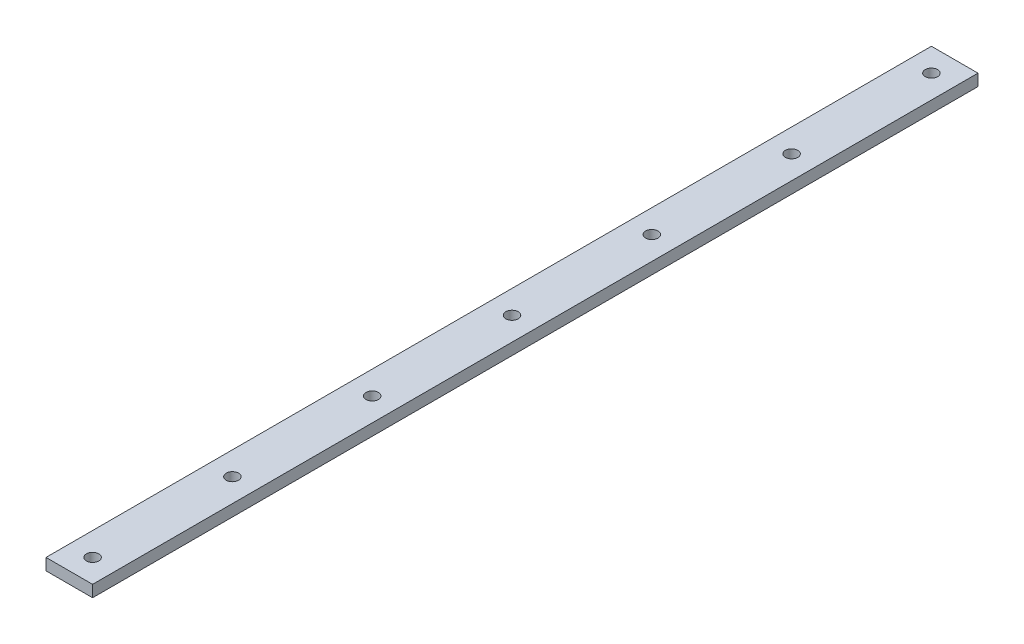
SolidWorks part; units mm, degrees
material "6061-T6 (SS)"
ref_plane "Front Plane" through (0, 0, 0) normal (0, 0, 1) x (1, 0, 0)
ref_plane "Top Plane" through (0, 0, 0) normal (0, 1, 0) x (1, 0, 0)
ref_plane "Right Plane" through (0, 0, 0) normal (1, 0, 0) x (0, 0, -1)
sketch "Sketch1" plane through (0, 0, 0) normal (0, 1, 0) x (1, 0, 0)
  line L1 (0, 0) -> (-25.4, 0)
  line L2 (0, 0) -> (0, 482.6)
  line L3 (0, 482.6) -> (-25.4, 482.6)
  line L4 (-25.4, 0) -> (-25.4, 482.6)
  dimension "D1" = 25.4
  dimension "D2" = 482.6
extrude "Boss-Extrude1" add sketch "Sketch1" along normal blind 6.35
hole_wizard "1/4 Clearance Hole1" positions "Sketch2" profile "Sketch3" hole size "1/4" standard "ANSI Inch" end condition through all
sketch "Sketch2" plane through (0, 6.35, 0) normal (0, 1, 0) x (1, 0, 0)
  line L0 (-25.4, 0) -> (0, 0) construction
  line L2 (0, 0) -> (0, 482.6) construction
  line L3 (0, 482.6) -> (-25.4, 482.6) construction
  point P0 (-12.7, 12.7)
  point P6 (-12.7, 88.9)
  point P7 (-12.7, 165.1)
  point P8 (-12.7, 241.3)
  point P9 (-12.7, 317.5)
  point P55 (-12.7, 568.0386)
  point P58 (-12.7, 568.567)
  point P59 (-12.7, 393.7)
  point P60 (-12.7, 469.9)
  point P61 (-12.7, 470.8349)
  dimension "D2" = 12.7
  dimension "D3" = 12.7
  dimension "D4" = 12.7
  dimension "D5" = 76.2
  dimension "D1" = 7
sketch "Sketch3" plane through (-12.7, 6.35, -12.7) normal (1, 0, 0) x (0, 0, 1)
  line L0 (0, 0) -> (0, 6.35)
  line L1 (0, 6.35) -> (3.3782, 6.35)
  line L2 (3.3782, 6.35) -> (3.3782, 0)
  line L5 (3.3782, 0) -> (0, 0)
  line L11 (0, -6.35) -> (0, 107.95) construction
  dimension "Thru Hole Dia." = 6.7564
  dimension "Thru Hole Depth" = 6.35
